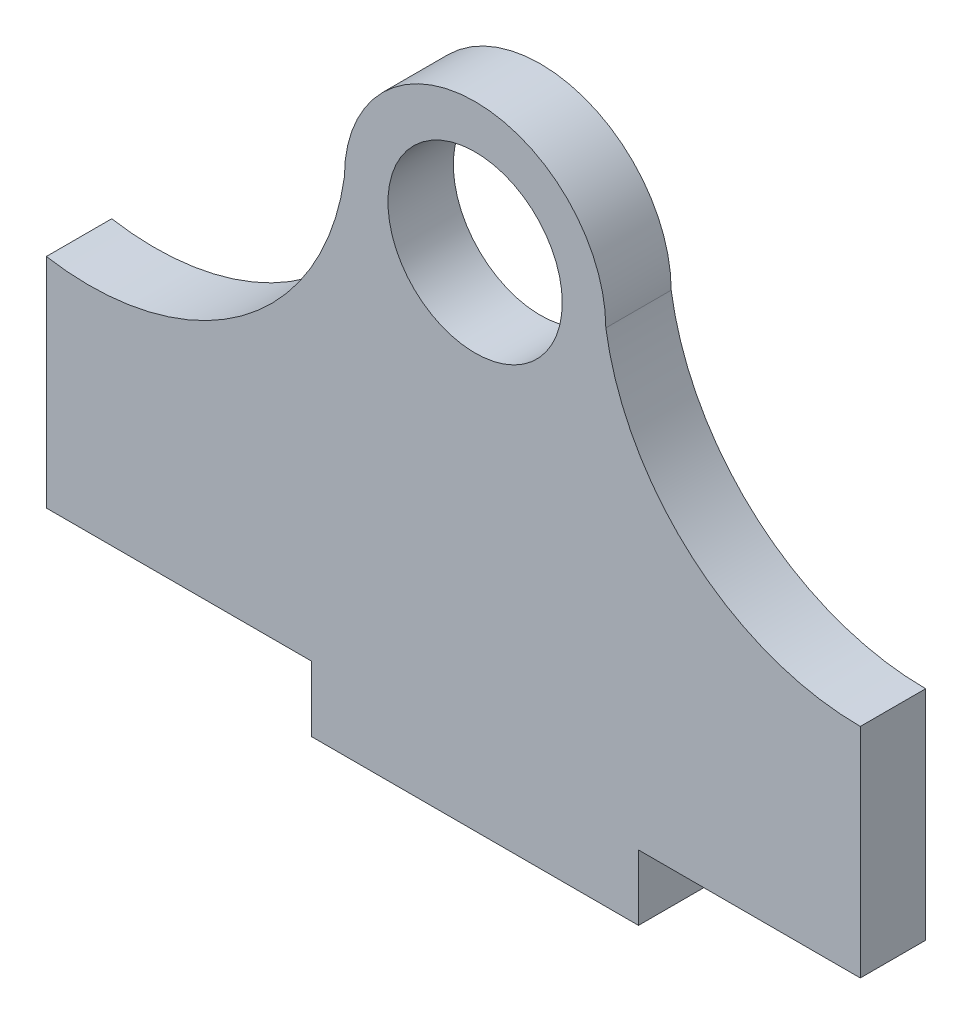
SolidWorks part; units mm, degrees
material "Cedar"
ref_plane "Front Plane" through (0, 0, 0) normal (0, 0, 1) x (1, 0, 0)
ref_plane "Top Plane" through (0, 0, 0) normal (0, 1, 0) x (1, 0, 0)
ref_plane "Right Plane" through (0, 0, 0) normal (1, 0, 0) x (0, 0, -1)
sketch "Sketch1" plane through (0, 0, 0) normal (0, 0, 1) x (1, 0, 0)
  line L0 (7.5, -20) -> (17.681, -20)
  line L2 (-19.681, -10) -> (-19.681, -20)
  line L3 (-19.681, -20) -> (-7.5, -20)
  line L4 (17.681, -10) -> (17.681, -20)
  line L5 (0, -17.5) -> (17.681, -20) construction
  line L6 (-3.0565, -18.7965) -> (17.681, -10) construction
  line L7 (-7.5, -23) -> (7.5, -23)
  line L8 (-7.5, -23) -> (-7.5, -20)
  line L10 (7.5, -23) -> (7.5, -20)
  line L12 (-7.5, -20) -> (0, -23) construction
  arc A0 (6, 0) -> (-6, 0) centre (0, 0) ccw
  arc A1 (-19.681, -10) -> (-6, 0) centre (-17.7057, 1.6561) ccw
  arc A2 (6, 0) -> (17.681, -10) centre (17.681, 1.8223) ccw
  circle A3 centre (0, 0) radius 4
  point P3 (0, -17.5)
  point P12 (0, -23)
  dimension "D1" = 20
  dimension "D2" = 12
  dimension "D5" = 8
  dimension "D3" = 10
  dimension "D4" = 15
  dimension "D6" = 10
extrude "Boss-Extrude1" add sketch "Sketch1" along normal blind 3
